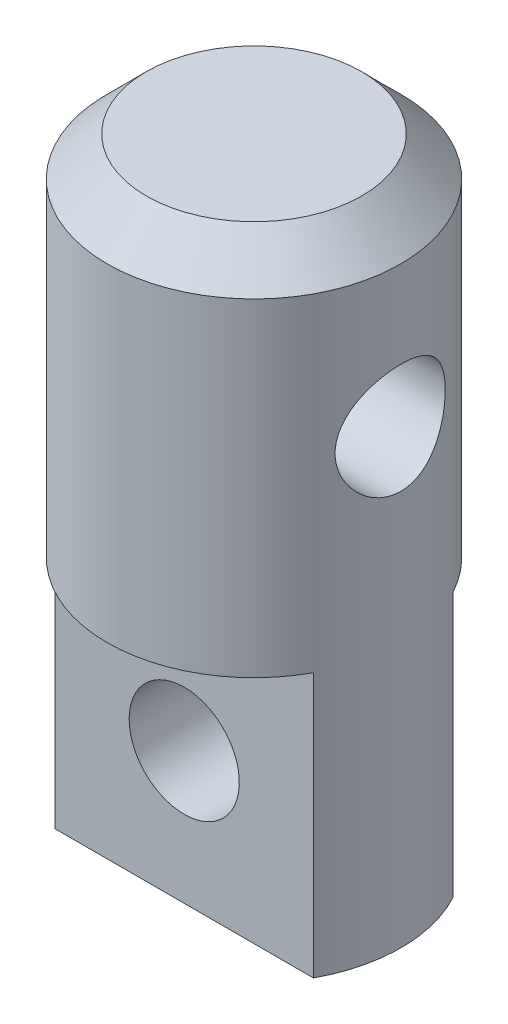
SolidWorks part; units mm, degrees
material "3003 Alloy"
ref_plane "Front Plane" through (0, 0, 0) normal (0, 0, 1) x (1, 0, 0)
ref_plane "Top Plane" through (0, 0, 0) normal (0, 1, 0) x (1, 0, 0)
ref_plane "Right Plane" through (0, 0, 0) normal (1, 0, 0) x (0, 0, -1)
sketch "Sketch1" plane through (0, 0, 0) normal (0, 1, 0) x (1, 0, 0)
  circle A0 centre (0, 0) radius 6
  dimension "D1" = 12
extrude "Boss-Extrude1" add sketch "Sketch1" against normal blind 25.8
chamfer "Chamfer1" distance 1.6 angle 45 1 edges at (0, 0, 6)
sketch "Sketch2" plane through (0, 0, 0) normal (1, 0, 0) x (0, 0, -1)
  line L0 (-2.85, -25.8) -> (2.85, -25.8)
  line L1 (-6, -25.8) -> (6, -25.8) construction
  line L2 (6, -15) -> (6, -25.8)
  line L4 (2.85, -15) -> (6, -15)
  line L5 (-2.85, -25.8) -> (-2.85, -15)
  line L6 (-6, -15) -> (-2.85, -15)
  line L7 (-6, -1.6) -> (-6, -25.8) construction
  line L8 (6, -25.8) -> (6, -1.6) construction
  line L9 (2.85, -25.8) -> (2.85, -15)
  line L10 (6, -25.8) -> (2.85, -25.8)
  line L11 (-2.85, -25.8) -> (-6, -25.8)
  line L12 (-6, -25.8) -> (-6, -15)
  dimension "D1" = 5.7
extrude "Cut-Extrude1" cut sketch "Sketch2" against normal through all both and the other way through all contours L9 L4 L2 L10 | L5 L6 L12 L11
sketch "Sketch3" plane through (0, 0, 2.85) normal (0, 0, 1) x (1, 0, 0)
  line L0 (-5.2799, -15) -> (5.2799, -25.8) construction
  line L1 (5.2799, -25.8) -> (-5.2799, -25.8) construction
  line L2 (5.2799, -25.8) -> (5.2799, -15) construction
  line L3 (-5.2799, -25.8) -> (5.2799, -15) construction
  circle A0 centre (0, -20.4) radius 2.25
  dimension "D1" = 4.5
extrude "Cut-Extrude2" cut sketch "Sketch3" against normal through all both and the other way through all
sketch "Sketch4" plane through (0, 0, 0) normal (1, 0, 0) x (0, 0, -1)
  line L0 (0, -1.6) -> (0, -7.4)
  line L1 (-6, -1.6) -> (6, -1.6) construction
  circle A0 centre (0, -7.4) radius 2.25
  dimension "D2" = 4.5
  dimension "D1" = 5.8
extrude "Cut-Extrude3" cut sketch "Sketch4" against normal through all both and the other way through all contours A0
